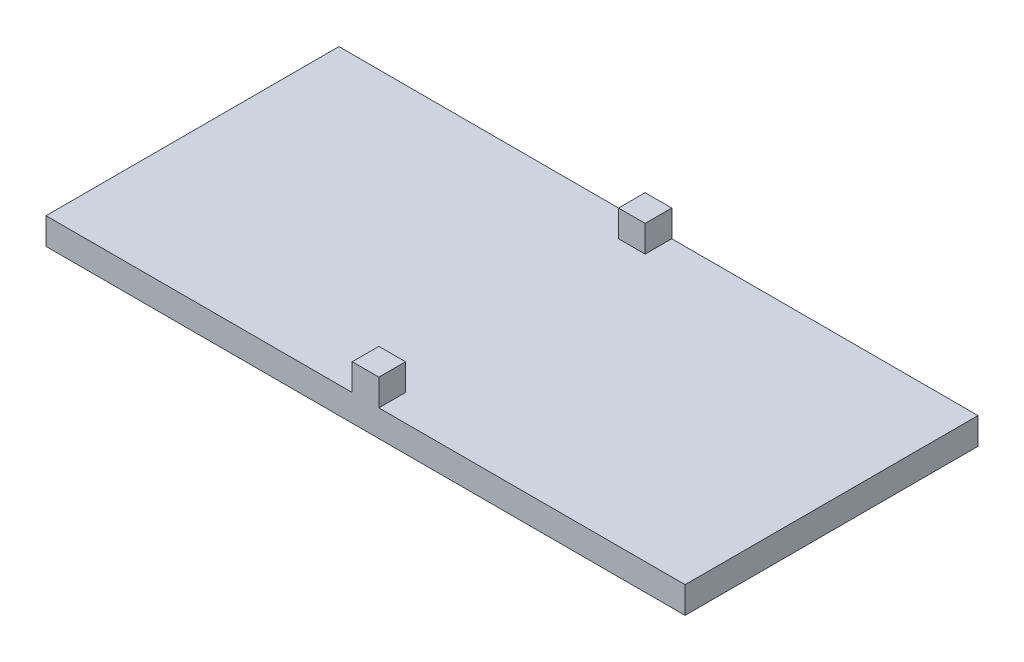
SolidWorks part; units mm, degrees
ref_plane "Plano frontal" through (0, 0, 0) normal (0, 0, 1) x (1, 0, 0)
ref_plane "Plano superior" through (0, 0, 0) normal (0, 1, 0) x (1, 0, 0)
ref_plane "Plano direito" through (0, 0, 0) normal (1, 0, 0) x (0, 0, -1)
sketch "Esboço1" plane through (0, 0, 0) normal (0, 1, 0) x (1, 0, 0)
  line L1 (-31.3285, 84.6107) -> (208.6715, 84.6107)
  line L2 (-31.3285, 84.6107) -> (-31.3285, -25.3893)
  line L3 (-31.3285, -25.3893) -> (208.6715, -25.3893)
  line L4 (208.6715, 84.6107) -> (208.6715, -25.3893)
  dimension "D1" = 240
  dimension "D2" = 110
extrude "Ressalto-extrusão1" add sketch "Esboço1" along normal blind 10
sketch "Esboço2" plane through (0, 10, 0) normal (0, 1, 0) x (1, 0, 0)
  line L0 (-31.3285, -25.3893) -> (208.6715, -25.3893) construction
  line L1 (83.6715, -25.3893) -> (93.6715, -25.3893)
  line L2 (83.6715, -25.3893) -> (83.6715, -15.3893)
  line L3 (83.6715, -15.3893) -> (93.6715, -15.3893)
  line L4 (93.6715, -25.3893) -> (93.6715, -15.3893)
  line L5 (208.6715, 84.6107) -> (-31.3285, 84.6107) construction
  line L6 (83.6715, 84.6107) -> (93.6715, 84.6107)
  line L7 (83.6715, 84.6107) -> (83.6715, 74.6107)
  line L8 (83.6715, 74.6107) -> (93.6715, 74.6107)
  line L9 (93.6715, 84.6107) -> (93.6715, 74.6107)
  line L10 (208.6715, -25.3893) -> (208.6715, 84.6107) construction
  line L11 (-31.3285, 84.6107) -> (-31.3285, -25.3893) construction
  dimension "D1" = 10
  dimension "D2" = 10
  dimension "D3" = 115
  dimension "D4" = 115
extrude "Ressalto-extrusão2" add sketch "Esboço2" along normal blind 10
